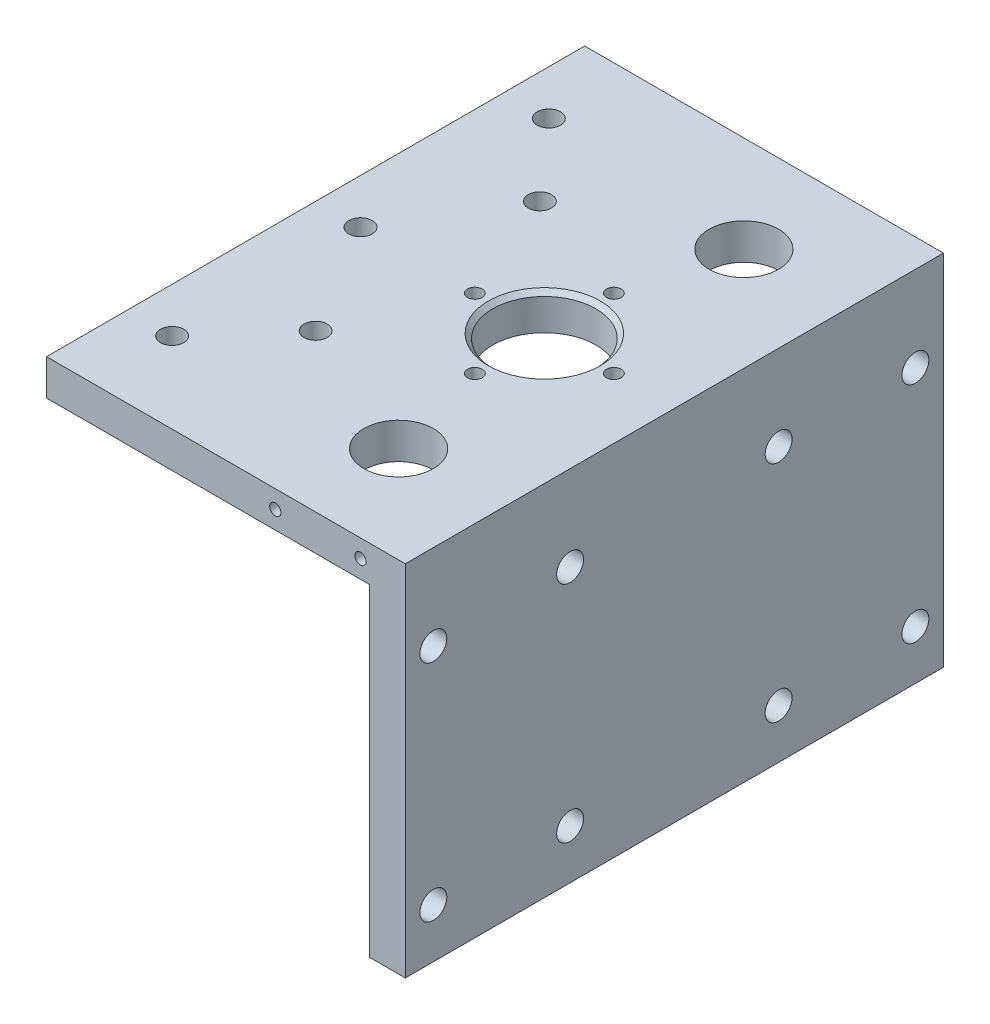
SolidWorks part; units mm, degrees
material "Lega 1060"
ref_plane "Piano frontale" through (0, 0, 0) normal (0, 0, 1) x (1, 0, 0)
ref_plane "Piano superiore" through (0, 0, 0) normal (0, 1, 0) x (1, 0, 0)
ref_plane "Piano destro" through (0, 0, 0) normal (1, 0, 0) x (0, 0, -1)
sketch "Schizzo1" plane through (0, 0, 0) normal (0, 0, 1) x (1, 0, 0)
  line L0 (0, 0) -> (-80, 0)
  line L1 (-80, 0) -> (-80, -8)
  line L2 (-80, -8) -> (-8, -8)
  line L3 (-8, -8) -> (-8, -80)
  line L4 (-8, -80) -> (0, -80)
  line L5 (0, -80) -> (0, 0)
  dimension "D1" = 80
  dimension "D2" = 80
  dimension "D3" = 8
  dimension "D4" = 8
extrude "Estrusione-Estrusione1" add sketch "Schizzo1" along normal blind 120
sketch "Schizzo12" plane through (0, 0, 0) normal (1, 0, 0) x (0, 0, -1)
  line L0 (0, -8) -> (-120, -8) construction
  line L1 (-21.5, 0) -> (-21.5, 40.839) construction
  line L5 (0, -80) -> (0, 0) construction
  line L6 (-120, -80) -> (-120, 0) construction
  line L7 (-120, 0) -> (0, 0) construction
  line L8 (-113.75, -19) -> (9.6992, -19) construction
  line L9 (-113.75, -69) -> (15.4001, -69) construction
  line L10 (-98.5, -47.4454) -> (-98.5, 40.839) construction
  circle A0 centre (-113.75, -19) radius 3
  circle A1 centre (-83.25, -19) radius 3
  circle A6 centre (-36.75, -19) radius 3
  circle A7 centre (-6.25, -19) radius 3
  circle A10 centre (-83.25, -69) radius 3
  circle A11 centre (-113.75, -69) radius 3
  circle A12 centre (-6.25, -69) radius 3
  circle A13 centre (-36.75, -69) radius 3
  dimension "D1" = 6
  dimension "D5" = 30.5
  dimension "D6" = 30.5
  dimension "D7" = 30.5
  dimension "D8" = 30.5
  dimension "D2" = 8
  dimension "D3" = 11
  dimension "D4" = 61
  dimension "D9" = 21.5
  dimension "D10" = 21.5
sketch "Schizzo6" plane through (0, 0, 0) normal (0, 1, 0) x (1, 0, 0)
  line L0 (-23, -0.5808) -> (-23, -110.5835) construction
  line L2 (0, 0) -> (-80, 0) construction
  line L3 (-32.5218, -60) -> (-8.0464, -60) construction
  line L6 (0, -120) -> (-80, -120) construction
  circle A0 centre (-23, -21.5) radius 7.75
  circle A1 centre (-23, -98.5) radius 7.75
  dimension "D2" = 15.5
  dimension "D1" = 15
  dimension "D3" = 21.5
  dimension "D4" = 38.5
extrude "Taglio-Estrusione2" cut sketch "Schizzo6" against normal up to next
sketch "Schizzo7" plane through (0, 0, 0) normal (0, 1, 0) x (1, 0, 0)
  line L0 (-83.5082, -60) -> (3.6289, -60) construction
  line L1 (0, -120) -> (-80, -120) construction
  line L2 (0, 0) -> (-80, 0) construction
  line L3 (-23, -21.5) -> (-23, -98.5) construction
  line L4 (0, -120) -> (0, 0) construction
  circle A0 centre (-29, -60) radius 11.5
  dimension "D1" = 23
  dimension "D3" = 29
extrude "Taglio-Estrusione3" cut sketch "Schizzo7" against normal up to next
hole_wizard "M4 Tapped Hole1" positions "Schizzo9" profile "Schizzo8" tap size "M4" standard "ISO" end condition through all
sketch "Schizzo9" plane through (0, 0, 0) normal (0, 1, 0) x (1, 0, 0)
  line L0 (-18.4657, -60) -> (-13.5, -60) construction
  line L2 (-29, -57.7684) -> (-29, -66.5063) construction
  circle A2 centre (-29, -60) radius 11.5 construction
  point P0 (-29, -44.5)
  point P2 (-44.5, -60)
  point P4 (-29, -75.5)
  point P8 (-13.5, -60)
  point P20 (-29, -60)
  dimension "D1" = 31
  dimension "D2" = 15.5
  dimension "D3" = 15.5
sketch "Schizzo8" plane through (-29, 0, 44.5) normal (1, 0, 0) x (0, 0, 1)
  line L0 (0, 0) -> (0, 80)
  line L1 (0, 80) -> (1.65, 80)
  line L2 (1.65, 80) -> (1.65, 0)
  line L5 (1.65, 0) -> (0, 0)
  line L11 (0, -6.35) -> (0, 107.95) construction
  dimension "Thread Major Dia." = 3.3
  dimension "Thru Tap Drill Depth" = 80
extrude "Taglio-Estrusione4" cut sketch "Schizzo12" against normal blind 10
sketch "Schizzo14" plane through (0, 0, 0) normal (0, 1, 0) x (1, 0, 0)
  line L0 (-70, 0) -> (-70, -120) construction
  line L1 (0, 0) -> (-80, 0) construction
  line L2 (0, -120) -> (-80, -120) construction
  line L3 (-80, -120) -> (-80, 0) construction
  line L4 (-55, 0) -> (-55, -120) construction
  line L5 (-23, -98.5) -> (-80, -98.5) construction
  line L6 (-80, -60) -> (0, -60) construction
  line L7 (0, -120) -> (0, 0) construction
  line L8 (-23, -21.5) -> (-80, -21.5) construction
  circle A0 centre (-70, -18) radius 2.6
  circle A1 centre (-70, -60) radius 2.6
  circle A2 centre (-70, -102) radius 2.6
  circle A3 centre (-55, -35) radius 2.6
  circle A4 centre (-55, -85) radius 2.6
  dimension "D3" = 5.2
  dimension "D4" = 5.2
  dimension "D5" = 5.2
  dimension "D6" = 5.2
  dimension "D7" = 5.2
  dimension "D1" = 10
  dimension "D2" = 25
  dimension "D8" = 35
  dimension "D9" = 35
  dimension "D10" = 25
  dimension "D11" = 42
  dimension "D12" = 15
extrude "Taglio-Estrusione5" cut sketch "Schizzo14" against normal blind 10
chamfer "Smusso2" distance 1 angle 45 1 edges at (-40.5, 0, 60)
sketch "Schizzo15" plane through (0, 0, 120) normal (0, 0, 1) x (1, 0, 0)
  line L0 (-80, -4) -> (0, -4) construction
  line L1 (-80, 0) -> (-80, -8) construction
  line L2 (0, -80) -> (0, 0) construction
  point P6 (-10, -4)
  point P7 (-29, -4)
  dimension "D1" = 10
  dimension "D2" = 19
hole_wizard "Foro filettato M3-1" positions "Schizzo17" profile "Schizzo16" tap size "M3" standard "ISO"
sketch "Schizzo17" plane through (0, 0, 120) normal (0, 0, 1) x (1, 0, 0)
  point P0 (-10, -4)
  point P3 (-29, -4)
sketch "Schizzo16" plane through (-10, -4, 120) normal (1, 0, 0) x (0, -1, 0)
  line L0 (0, 0) -> (0, 10.7511)
  line L1 (0, 10.7511) -> (1.25, 10)
  line L2 (1.25, 10) -> (1.25, 0)
  line L5 (1.25, 0) -> (0, 0)
  line L10 (0, 10.7511) -> (-1.25, 10) construction
  line L11 (0, -6.35) -> (0, 107.95) construction
  dimension "Tap Drill Dia." = 2.5
  dimension "Tap Drill Depth" = 10
  dimension "Drill Angle" = 118
cosmetic thread "Filettatura del foro1" parameters "D1"=8, "D2"=3
cosmetic thread "Filettatura del foro2" parameters "D1"=8, "D2"=3
sketch "Sketch1" plane through (0, 0, 0) normal (1, 0, 0) x (0, 0, -1)
  line L0 (0, -80) -> (0, 0) construction
  point P0 (0, -8)
  dimension "D1" = 8
